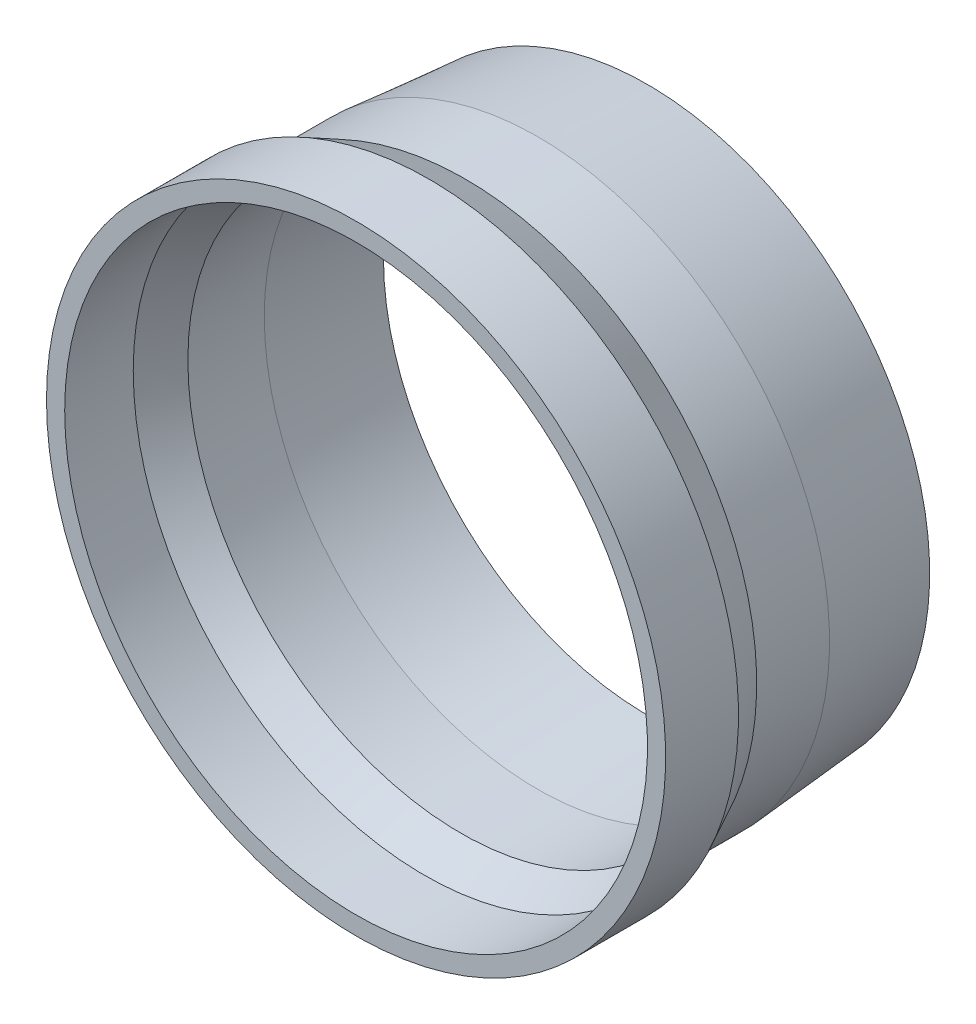
SolidWorks part; units mm, degrees
ref_plane "Front Plane" through (0, 0, 0) normal (0, 0, 1) x (1, 0, 0)
ref_plane "Top Plane" through (0, 0, 0) normal (0, 1, 0) x (1, 0, 0)
ref_plane "Right Plane" through (0, 0, 0) normal (1, 0, 0) x (0, 0, -1)
sketch "Sketch1" plane through (0, 0, 0) normal (1, 0, 0) x (0, 0, -1)
  line L0 (0, 0) -> (-126.0707, 0) construction
  line L1 (-38.8495, 50.8) -> (-32.4995, 47.625)
  line L3 (-31.75, 50.8) -> (-38.1, 53.975)
  line L5 (-38.1, 53.975) -> (-50.8, 53.975)
  line L6 (-50.8, 53.975) -> (-50.8, 50.8)
  line L7 (-50.8, 50.8) -> (-38.8495, 50.8)
  line L8 (-31.75, 50.8) -> (-19.05, 50.8)
  line L9 (-19.05, 50.8) -> (0, 49.2125)
  line L10 (0, 49.2125) -> (0, 46.0265)
  line L11 (0, 46.0265) -> (-19.1821, 47.625)
  line L12 (-19.1821, 47.625) -> (-32.4995, 47.625)
  point P13 (0, 47.6195)
  dimension "D1" = 3.175
  dimension "D2" = 3.175
  dimension "D3" = 101.6
  dimension "D4" = 101.6
  dimension "D5" = 3.175
  dimension "D6" = 12.7
  dimension "D7" = 98.425
  dimension "D8" = 3.175
  dimension "D9" = 12.7
  dimension "D10" = 19.05
  dimension "D11" = 6.35
revolve "Revolve1" add sketch "Sketch1" angle 360 about L0
